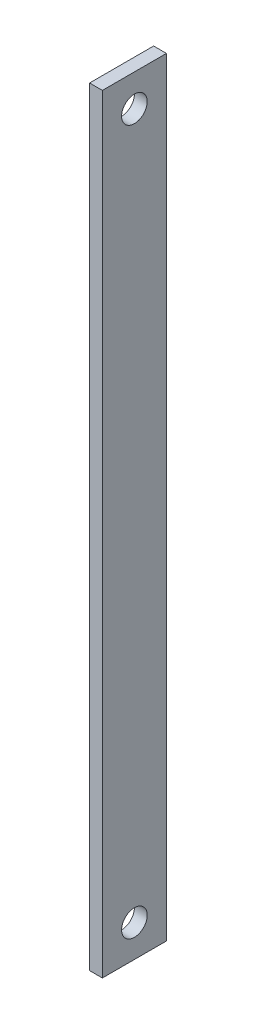
SolidWorks part; units mm, degrees
ref_plane "Front Plane" through (0, 0, 0) normal (0, 0, 1) x (1, 0, 0)
ref_plane "Top Plane" through (0, 0, 0) normal (0, 1, 0) x (1, 0, 0)
ref_plane "Right Plane" through (0, 0, 0) normal (1, 0, 0) x (0, 0, -1)
sketch "Sketch1" plane through (0, 0, 0) normal (1, 0, 0) x (0, 0, -1)
  line L1 (0, 0) -> (10, 0)
  line L2 (0, 0) -> (0, 120)
  line L3 (0, 120) -> (10, 120)
  line L4 (10, 0) -> (10, 120)
  circle A0 centre (5, 115) radius 2
  circle A1 centre (5, 5) radius 2
  dimension "D3" = 4
  dimension "D6" = 4
  dimension "D1" = 10
  dimension "D2" = 120
  dimension "D4" = 5
  dimension "D5" = 5
  dimension "D7" = 5
  dimension "D8" = 5
extrude "Boss-Extrude1" add sketch "Sketch1" along normal blind 2
